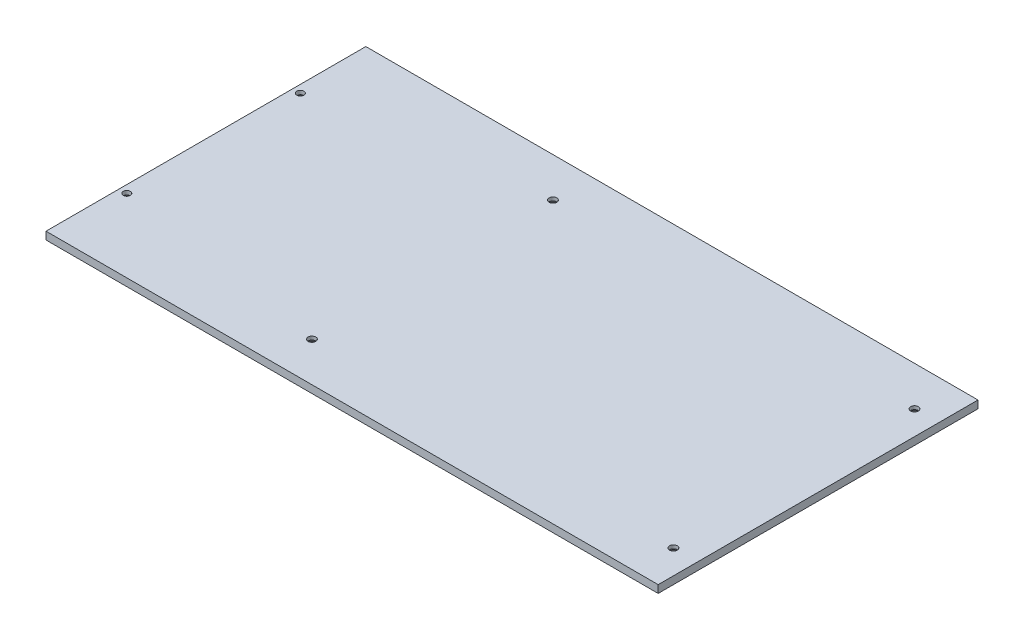
SolidWorks part; units mm, degrees
material "6061-T6 (SS)"
ref_plane "Front Plane" through (0, 0, 0) normal (0, 0, 1) x (1, 0, 0)
ref_plane "Top Plane" through (0, 0, 0) normal (0, 1, 0) x (1, 0, 0)
ref_plane "Right Plane" through (0, 0, 0) normal (1, 0, 0) x (0, 0, -1)
other "Configuration Table"
sketch "Sketch1" plane through (0, 0, 0) normal (0, 1, 0) x (1, 0, 0)
  line L1 (0, 0) -> (254, 0)
  line L2 (0, 0) -> (0, 132.7)
  line L3 (0, 132.7) -> (254, 132.7)
  line L4 (254, 0) -> (254, 132.7)
  dimension "D1" = 132.7
  dimension "D2" = 254
extrude "Boss-Extrude1" add sketch "Sketch1" along normal blind 3.175
sketch "Base PSU Hole Pattern" plane through (0, 0, 0) normal (0, -1, 0) x (-1, 0, 0)
  line L0 (-254, 66.35) -> (-169, 66.35) construction
  line L1 (-254, 0) -> (-254, 132.7) construction
  line L3 (-94, 16.35) -> (-244, 16.35)
  line L4 (-94, 16.35) -> (-94, 116.35)
  line L5 (-94, 116.35) -> (-244, 116.35)
  line L6 (-244, 16.35) -> (-244, 116.35)
  line L7 (-94, 16.35) -> (-244, 116.35) construction
  line L8 (-94, 116.35) -> (-244, 16.35) construction
  dimension "D1" = 85
  dimension "D2" = 100
  dimension "D3" = 150
sketch "Sketch3" plane through (0, 0, 0) normal (0, -1, 0) x (-1, 0, 0)
  point P3 (-3.175, 102.35)
  point P12 (-3.175, 30.35)
sketch "Sketch5" plane through (0, 0, 0) normal (0, -1, 0) x (-1, 0, 0)
  point P0 (-244, 116.35)
  point P3 (-94, 116.35)
  point P6 (-94, 16.35)
  point P9 (-244, 16.35)
hole_wizard "CSK for M3 SFHCS1" positions "Sketch5" profile "Sketch6" countersink size "M3" standard "ANSI Metric"
sketch "Sketch6" plane through (244, 0, -116.35) normal (1, 0, 0) x (0, 0, -1)
  line L0 (0, 0) -> (0, 11.9342)
  line L1 (0, 11.9342) -> (1.6, 10.9728)
  line L2 (1.6, 10.9728) -> (1.6, 1.76)
  line L3 (1.6, 1.76) -> (3.36, 0)
  line L5 (3.36, 0) -> (0, 0)
  line L6 (-1.6, 1.76) -> (-3.36, 0) construction
  line L10 (0, 11.9342) -> (-1.6, 10.9728) construction
  line L11 (0, -6.35) -> (0, 107.95) construction
  dimension "Hole Dia." = 3.2
  dimension "Hole Depth" = 10.9728
  dimension "Near C'Sink Dia." = 6.72
  dimension "Near C'Sink Angle" = 90
  dimension "Drill Angle" = 118
sketch "Wall Hole Pattern" plane through (0, 0, 0) normal (0, -1, 0) x (1, 0, 0)
  line L0 (6.35, -3.175) -> (6.35, -129.525) construction
  line L5 (0, -132.7) -> (0, 0) construction
  line L6 (6.35, -3.175) -> (6.35, 0) construction
  line L8 (0, 0) -> (254, 0) construction
  line L9 (6.35, -129.525) -> (47.625, -129.525) construction
  line L10 (47.625, -129.525) -> (88.9, -129.525) construction
  line L11 (88.9, -129.525) -> (130.175, -129.525) construction
  line L12 (6.35, -129.525) -> (6.35, -132.7) construction
  line L13 (254, -132.7) -> (0, -132.7) construction
  line L14 (130.175, -129.525) -> (171.45, -129.525) construction
  line L15 (171.45, -129.525) -> (212.725, -129.525) construction
  line L16 (212.725, -129.525) -> (254, -129.525) construction
  line L17 (254, 0) -> (254, -132.7) construction
  line L18 (6.35, -3.175) -> (47.625, -3.175) construction
  line L19 (47.625, -3.175) -> (88.9, -3.175) construction
  line L20 (88.9, -3.175) -> (130.175, -3.175) construction
  line L21 (130.175, -3.175) -> (171.45, -3.175) construction
  line L22 (171.45, -3.175) -> (212.725, -3.175) construction
  line L23 (212.725, -3.175) -> (254, -3.175) construction
  dimension "D1" = 6.35
  dimension "D2" = 3.175
hole_wizard "CSK for #4 Flat Head Machine Screw1" positions "Sketch3" profile "Sketch4" countersink size "#4" standard "ANSI Inch"
sketch "Sketch4" plane through (3.175, 0, -102.35) normal (1, 0, 0) x (0, 0, -1)
  line L0 (0, 0) -> (0, 11.858)
  line L1 (0, 11.858) -> (1.4732, 10.9728)
  line L2 (1.4732, 10.9728) -> (1.4732, 1.5925)
  line L3 (1.4732, 1.5925) -> (2.8575, 0)
  line L5 (2.8575, 0) -> (0, 0)
  line L6 (-1.4732, 1.5925) -> (-2.8575, 0) construction
  line L10 (0, 11.858) -> (-1.4732, 10.9728) construction
  line L11 (0, -6.35) -> (0, 107.95) construction
  dimension "Hole Dia." = 2.9464
  dimension "Hole Depth" = 10.9728
  dimension "Near C'Sink Dia." = 5.715
  dimension "Near C'Sink Angle" = 82
  dimension "Drill Angle" = 118
equation "\"D1@Sketch1\"=120mm+2*0.25in"
